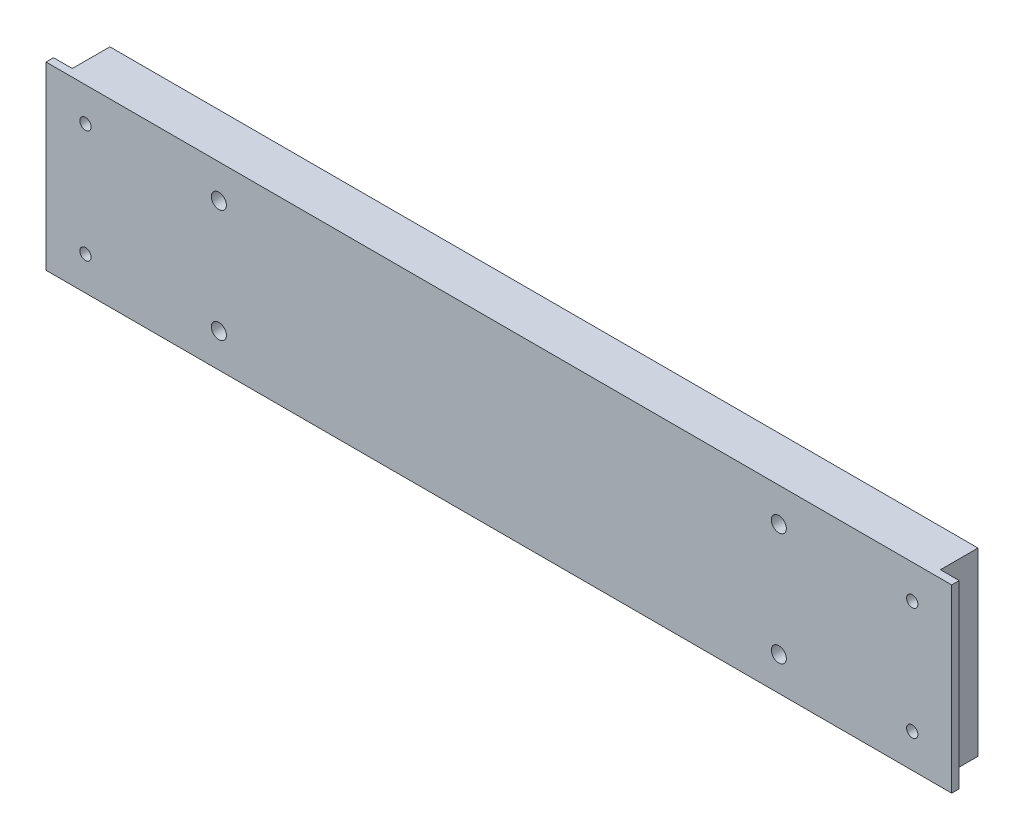
SolidWorks part; units mm, degrees
ref_plane "Plan de face" through (0, 0, 0) normal (0, 0, 1) x (1, 0, 0)
ref_plane "Plan de dessus" through (0, 0, 0) normal (0, 1, 0) x (1, 0, 0)
ref_plane "Plan de droite" through (0, 0, 0) normal (1, 0, 0) x (0, 0, -1)
sketch "Esquisse1" plane through (0, 0, 0) normal (0, 0, 1) x (1, 0, 0)
  line L0 (0, 0) -> (241, 0)
  line L1 (0, 0) -> (0, -48)
  line L2 (0, -48) -> (241, -48)
  line L3 (241, 0) -> (241, -48)
  line L4 (10.5, 0) -> (10.5, -48) construction
  line L7 (0, -24) -> (74.1871, -24) construction
  circle A0 centre (230.5, -39) radius 1.5
  circle A1 centre (10.5, -9) radius 1.5
  circle A2 centre (10.5, -39) radius 1.5
  circle A3 centre (230.5, -9) radius 1.5
  circle A5 centre (195, -39) radius 2
  circle A6 centre (46, -9) radius 2
  circle A8 centre (46, -39) radius 2
  circle A9 centre (195, -9) radius 2
extrude "Extrusion1" add sketch "Esquisse1" along normal blind 12
sketch "Esquisse2" plane through (0, 0, 0) normal (0, 1, 0) x (1, 0, 0)
  line L0 (120.5, -12) -> (120.5, 17.6208) construction
  line L2 (241, -12) -> (0, -12) construction
  line L3 (5, -10) -> (0, -10)
  line L4 (0, -12) -> (0, 0) construction
  line L5 (0, -10) -> (0, 0)
  line L6 (0, 0) -> (5, 0)
  line L7 (241, 0) -> (0, 0) construction
  line L8 (5, 0) -> (5, -10)
  line L9 (236, 0) -> (236, -10)
  line L10 (241, 0) -> (236, 0)
  line L11 (241, -10) -> (241, 0)
  line L12 (236, -10) -> (241, -10)
extrude "Extrusion2" cut sketch "Esquisse2" against normal through all
